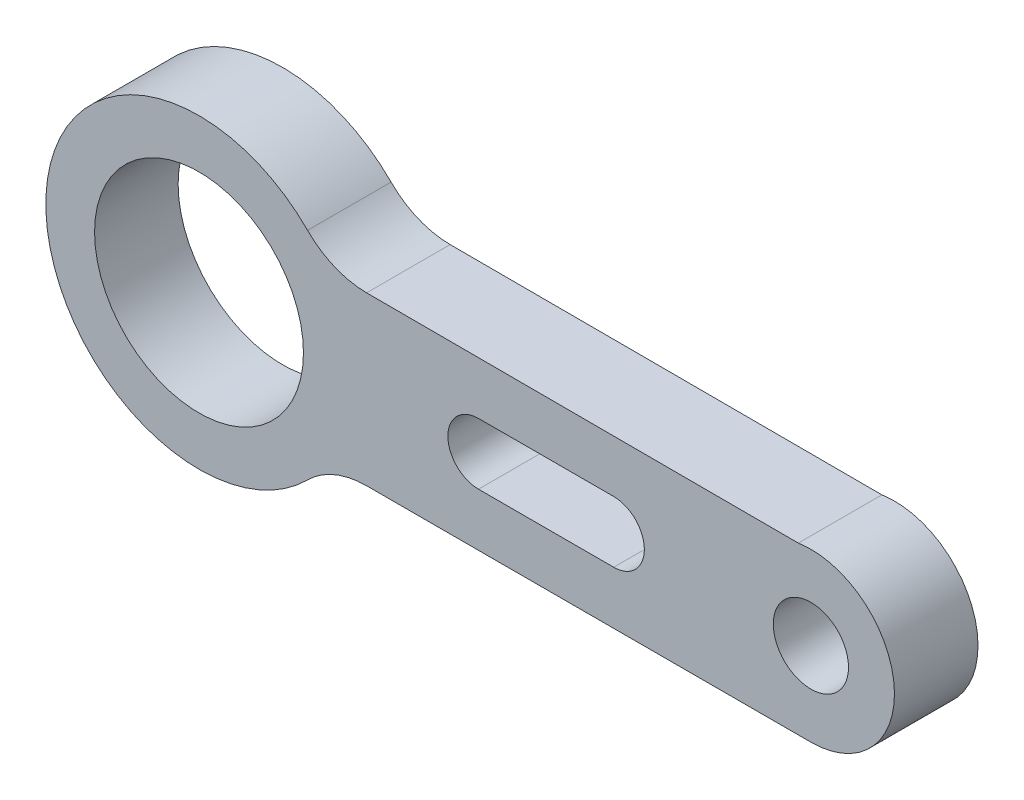
SolidWorks part; units mm, degrees
ref_plane "Plan de face" through (0, 0, 0) normal (0, 0, 1) x (1, 0, 0)
ref_plane "Plan de dessus" through (0, 0, 0) normal (0, 1, 0) x (1, 0, 0)
ref_plane "Plan de droite" through (0, 0, 0) normal (1, 0, 0) x (0, 0, -1)
sketch "Esquisse6" plane through (0, 0, 0) normal (0, 0, 1) x (1, 0, 0)
  line L0 (-3.988, 21.4662) -> (-25.9583, 21.4662) construction
  line L1 (-3.988, 18.4662) -> (-19.941, 18.4633)
  line L2 (-4.4396, 24.432) -> (-19.9406, 24.4633)
  line L3 (-15.922, 21.4662) -> (-11.0684, 21.4662) construction
  line L4 (-15.922, 22.5662) -> (-11.0684, 22.5662)
  line L5 (-15.922, 20.3662) -> (-11.0684, 20.3662)
  arc A0 (-3.988, 18.4662) -> (-4.4396, 24.432) centre (-3.988, 21.4662) ccw
  arc A1 (-22.0606, 25.3467) -> (-22.0644, 17.582) centre (-25.9583, 21.4662) ccw
  circle A2 centre (-3.988, 21.4662) radius 1.35
  circle A3 centre (-25.9583, 21.4662) radius 3.75
  arc A4 (-19.941, 18.4633) -> (-22.0644, 17.582) centre (-19.9404, 15.4633) ccw
  arc A5 (-19.9406, 24.4633) -> (-22.0606, 25.3467) centre (-19.9345, 27.4633) cw
  arc A6 (-15.922, 22.5662) -> (-15.922, 20.3662) centre (-15.922, 21.4662) ccw
  arc A7 (-11.0684, 20.3662) -> (-11.0684, 22.5662) centre (-11.0684, 21.4662) ccw
  point P2 (-14.9747, 21.4662)
  point P17 (-13.4952, 21.4662)
  dimension "D1" = 2.7
  dimension "D2" = 3
  dimension "D3" = 7.5
  dimension "D4" = 11
  dimension "D5" = 3
  dimension "D6" = 1.1
extrude "Boss.-Extru.6" add sketch "Esquisse6" along normal blind 3 separate body
